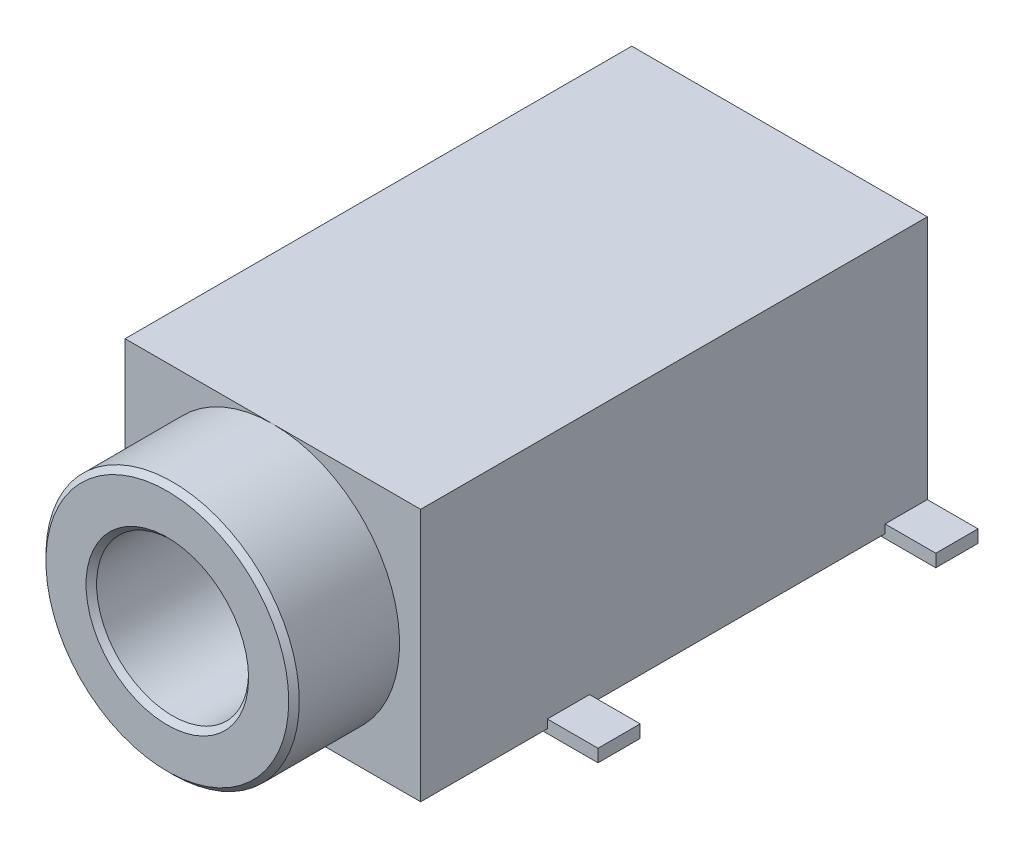
SolidWorks part; units mm, degrees
ref_plane "Plan de face" through (0, 0, 0) normal (0, 0, 1) x (1, 0, 0)
ref_plane "Plan de dessus" through (0, 0, 0) normal (0, 1, 0) x (1, 0, 0)
ref_plane "Plan de droite" through (0, 0, 0) normal (1, 0, 0) x (0, 0, -1)
sketch "Esquisse1" plane through (0, 0, 0) normal (0, 0, 1) x (1, 0, 0)
  circle A0 centre (0, 3) radius 3
  point P2 (0, 0)
  dimension "D1" = 6
extrude "Boss.-Extru.1" add sketch "Esquisse1" along normal blind 2.5
sketch "Esquisse2" plane through (0, 0, 0) normal (0, 0, 1) x (1, 0, 0)
  line L1 (3.5, 0) -> (-3.5, 0)
  line L2 (3.5, 0) -> (3.5, 6)
  line L3 (3.5, 6) -> (-3.5, 6)
  line L4 (-3.5, 0) -> (-3.5, 6)
  point P4 (0, 6)
  point P6 (3.5, 7.1122)
  dimension "D1" = 6
  dimension "D2" = 7
extrude "Boss.-Extru.2" add sketch "Esquisse2" against normal blind 12
sketch "Esquisse4" plane through (0, 0, 2.5) normal (0, 0, 1) x (1, 0, 0)
  circle A0 centre (0, 3) radius 1.8
  dimension "D1" = 3.6
extrude "Enlèv. mat.-Extru.2" cut sketch "Esquisse4" against normal through all
chamfer "Chanfrein2" distance 0.125 angle 45 2 edges at (1.8, 3, 2.5) (3, 3, 2.5)
sketch "Esquisse5" plane through (0, 0, 0) normal (0, -1, 0) x (1, 0, 0)
  circle A0 centre (0, -2) radius 0.55
  circle A1 centre (0, -9) radius 0.55
  dimension "D1" = 1.1
  dimension "D2" = 7
  dimension "D3" = 2
extrude "Boss.-Extru.3" add sketch "Esquisse5" along normal blind 1
fillet "Congé1" radius 0.1 2 edges at (0, -1, -2.55) (0, -1, -9.55)
sketch "Esquisse6" plane through (0, 0, 0) normal (0, -1, 0) x (1, 0, 0)
  line L0 (-3.5, -12) -> (-3.5, 0) construction
  line L1 (-3, -4) -> (-4.7, -4)
  line L2 (-3, -4) -> (-3, -3)
  line L3 (-3, -3) -> (-4.7, -3)
  line L4 (-4.7, -4) -> (-4.7, -3)
  line L5 (0, 0) -> (3.5, 0) construction
  line L6 (-4.7, -11) -> (-3, -11)
  line L7 (-4.7, -11) -> (-4.7, -12)
  line L8 (-4.7, -12) -> (-3, -12)
  line L9 (-3, -11) -> (-3, -12)
  point P4 (-4.7, -3.5)
  point P12 (-4.8352, -10.1189)
  point P13 (-2.7471, -8.9681)
  point P16 (-4.7, -11.5)
  dimension "D1" = 1
  dimension "D2" = 4.7
  dimension "D3" = 3.5
  dimension "D4" = 0.5
  dimension "D5" = 1
  dimension "D6" = 11.5
extrude "Boss.-Extru.4" add sketch "Esquisse6" along normal blind 0.1 and the other way blind 0.2
mirror "Symétrie1" about plane through (0, 0, 0) normal (1, 0, 0) of "Boss.-Extru.4"
sketch "Esquisse7" plane through (0, 0, 0) normal (0, -1, 0) x (1, 0, 0)
  line L0 (-3, -12) -> (3, -12) construction
  line L1 (-0.5, -11.5) -> (0.5, -11.5)
  line L2 (-0.5, -11.5) -> (-0.5, -13.2)
  line L3 (-0.5, -13.2) -> (0.5, -13.2)
  line L4 (0.5, -11.5) -> (0.5, -13.2)
  line L5 (0, -13.2) -> (0, -12) construction
  dimension "D1" = 1
  dimension "D2" = 1.7
  dimension "D3" = 1.2
extrude "Boss.-Extru.5" add sketch "Esquisse7" along normal blind 0.1 and the other way blind 0.2
